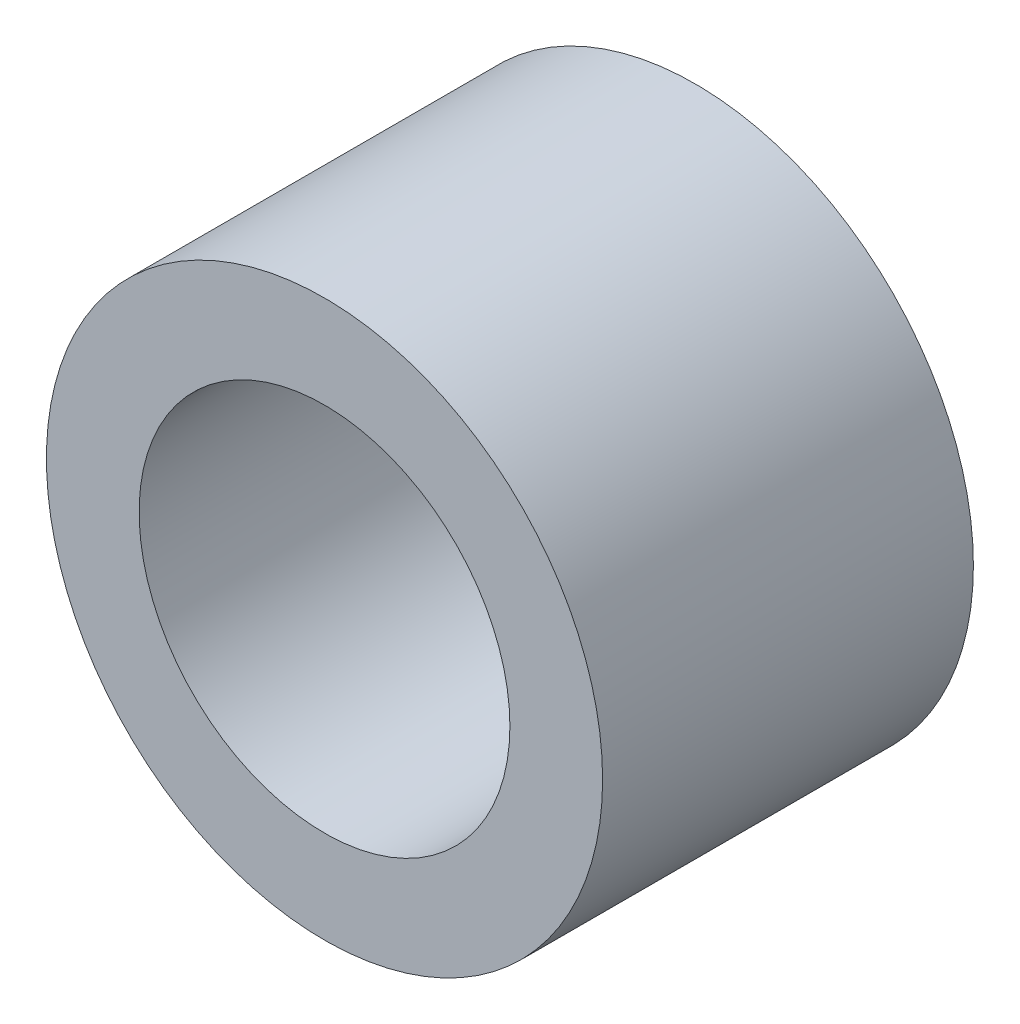
SolidWorks part; units mm, degrees
material "Alloy Steel"
ref_plane "Front Plane" through (0, 0, 0) normal (0, 0, 1) x (1, 0, 0)
ref_plane "Top Plane" through (0, 0, 0) normal (0, 1, 0) x (1, 0, 0)
ref_plane "Right Plane" through (0, 0, 0) normal (1, 0, 0) x (0, 0, -1)
sketch "Sketch1" plane through (0, 0, 0) normal (0, 0, 1) x (1, 0, 0)
  circle A0 centre (0, 0) radius 5
  circle A1 centre (0, 0) radius 7.5
  dimension "D1" = 15
  dimension "D2" = 10
extrude "Boss-Extrude1" add sketch "Sketch1" along normal blind 10
